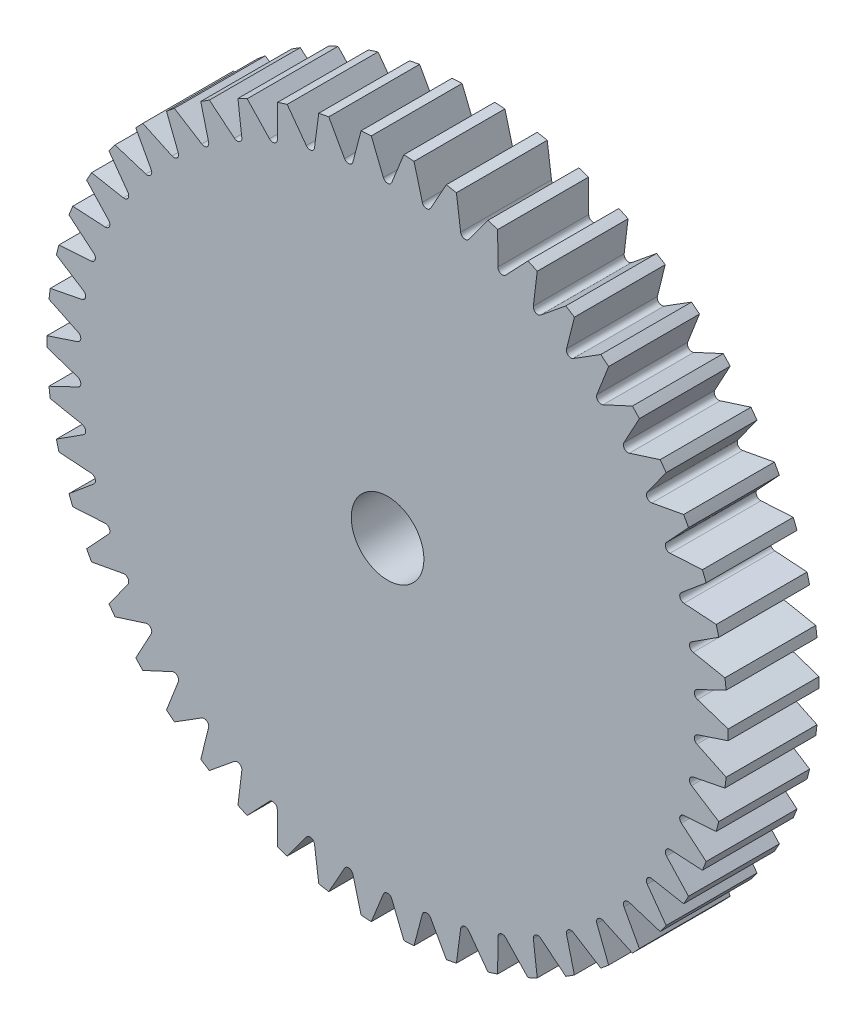
SolidWorks part; units mm, degrees
ref_plane "Front Plane" through (0, 0, 0) normal (0, 0, 1) x (1, 0, 0)
ref_plane "Top Plane" through (0, 0, 0) normal (0, 1, 0) x (1, 0, 0)
ref_plane "Right Plane" through (0, 0, 0) normal (1, 0, 0) x (0, 0, -1)
sketch "Sketch1" plane through (0, 0, 0) normal (0, 0, 1) x (1, 0, 0)
  circle A0 centre (0, 0) radius 37.5
  circle A1 centre (0, 0) radius 4
  dimension "D1" = 75
  dimension "D2" = 8
extrude "Boss-Extrude1" add sketch "Sketch1" along normal blind 10
sketch "Sketch2" plane through (0, 0, 10) normal (0, 0, 1) x (1, 0, 0)
  line L0 (-3.8404, 42.5395) -> (-0.4638, 34.1521)
  line L1 (0.4638, 34.1521) -> (3.8404, 42.5395)
  line L2 (3.8404, 42.5395) -> (-3.8404, 42.5395)
  arc A0 (-0.4638, 34.1521) -> (0.4638, 34.1521) centre (0, 34.3389) ccw
  point P6 (0, 33)
  dimension "D4" = 0.5
  dimension "D1" = 33
  dimension "D2" = 7.6808
  dimension "D3" = 9.5395
extrude "Cut-Extrude1" cut sketch "Sketch2" against normal through all
pattern_circular "CirPattern1" count 50 over 360 about axis through (0, 0, 0) along (0, 0, 1) of "Cut-Extrude1"
